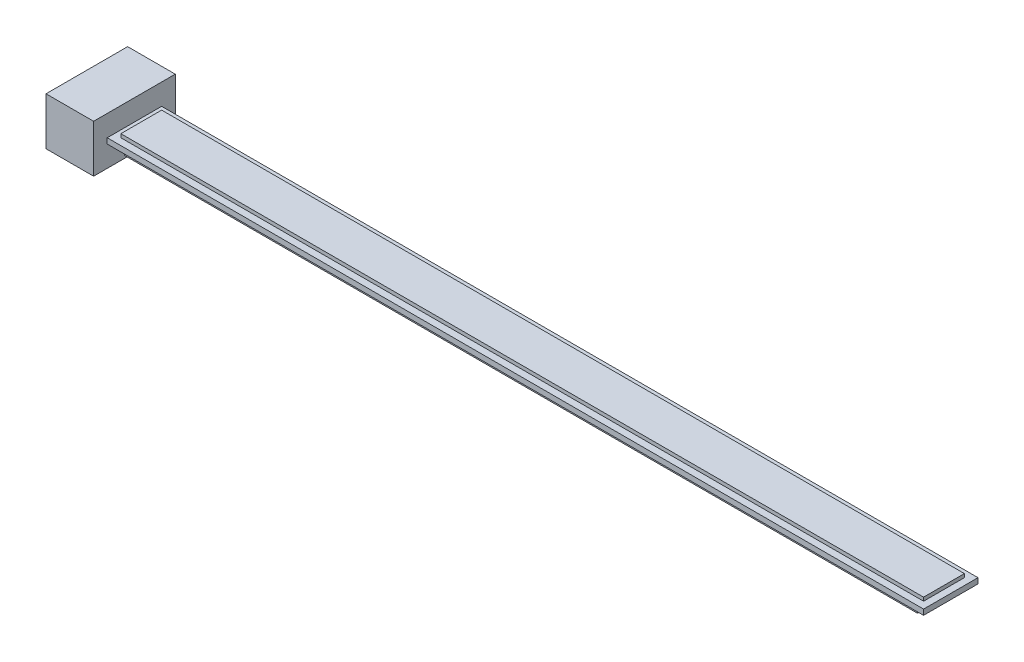
SolidWorks part; units mm, degrees
ref_plane "Front Plane" through (0, 0, 0) normal (0, 0, 1) x (1, 0, 0)
ref_plane "Top Plane" through (0, 0, 0) normal (0, 1, 0) x (1, 0, 0)
ref_plane "Right Plane" through (0, 0, 0) normal (1, 0, 0) x (0, 0, -1)
sketch "Sketch1" plane through (0, 0, 0) normal (0, 0, 1) x (1, 0, 0)
  line L1 (-17.5, 17.5) -> (17.5, 17.5)
  line L2 (-17.5, 17.5) -> (-17.5, -17.5)
  line L3 (-17.5, -17.5) -> (17.5, -17.5)
  line L4 (17.5, 17.5) -> (17.5, -17.5)
  line L5 (-17.5, 17.5) -> (17.5, -17.5) construction
  line L6 (-17.5, -17.5) -> (17.5, 17.5) construction
  point P0 (0, 0)
  dimension "D1" = 35
  dimension "D2" = 35
extrude "Boss-Extrude1" add sketch "Sketch1" along normal blind 60 contours L2 L1 L4 L3
ref_plane "Plane1" through (0, 0, 30) normal (0, 0, 1) x (1, 0, 0)
sketch "Sketch2" plane through (17.5, 0, 0) normal (1, 0, 0) x (0, 0, -1)
  line L0 (-30, 19.25) -> (-30, -19.25) construction
  line L1 (-50, 2) -> (-10, 2)
  line L2 (-50, 2) -> (-50, -2)
  line L3 (-50, -2) -> (-10, -2)
  line L4 (-10, 2) -> (-10, -2)
  line L5 (-50, 2) -> (-10, -2) construction
  line L6 (-50, -2) -> (-10, 2) construction
  point P0 (-30, 0)
  dimension "D1" = 4
  dimension "D2" = 40
extrude "Boss-Extrude2" add sketch "Sketch2" along normal blind 600
sketch "Sketch3" plane through (0, 2, 0) normal (0, 1, 0) x (1, 0, 0)
  line L0 (-19.25, -30) -> (19.25, -30) construction
  line L1 (22.5, -15) -> (612.5, -15)
  line L2 (22.5, -15) -> (22.5, -45)
  line L3 (22.5, -45) -> (612.5, -45)
  line L4 (612.5, -15) -> (612.5, -45)
  line L5 (22.5, -15) -> (612.5, -45) construction
  line L6 (22.5, -45) -> (612.5, -15) construction
  point P0 (317.5, -30)
  dimension "D1" = 30
  dimension "D2" = 590
extrude "Boss-Extrude3" add sketch "Sketch3" along normal blind 2.6 contours L2 L3 L4 L1
sketch "Sketch4" plane through (0, -2, 0) normal (0, -1, 0) x (1, 0, 0)
  line L1 (26.1029, 45.9107) -> (608.8971, 45.9107)
  line L2 (26.1029, 45.9107) -> (26.1029, 36.8189)
  line L3 (26.1029, 36.8189) -> (608.8971, 36.8189)
  line L4 (608.8971, 45.9107) -> (608.8971, 36.8189)
  line L5 (26.1029, 45.9107) -> (608.8971, 36.8189) construction
  line L6 (26.1029, 36.8189) -> (608.8971, 45.9107) construction
extrude "Boss-Extrude6" add sketch "Sketch4" along normal blind 5
mirror "Mirror1" about plane through (0, 0, 30) normal (0, 0, 1) of "Boss-Extrude6"
